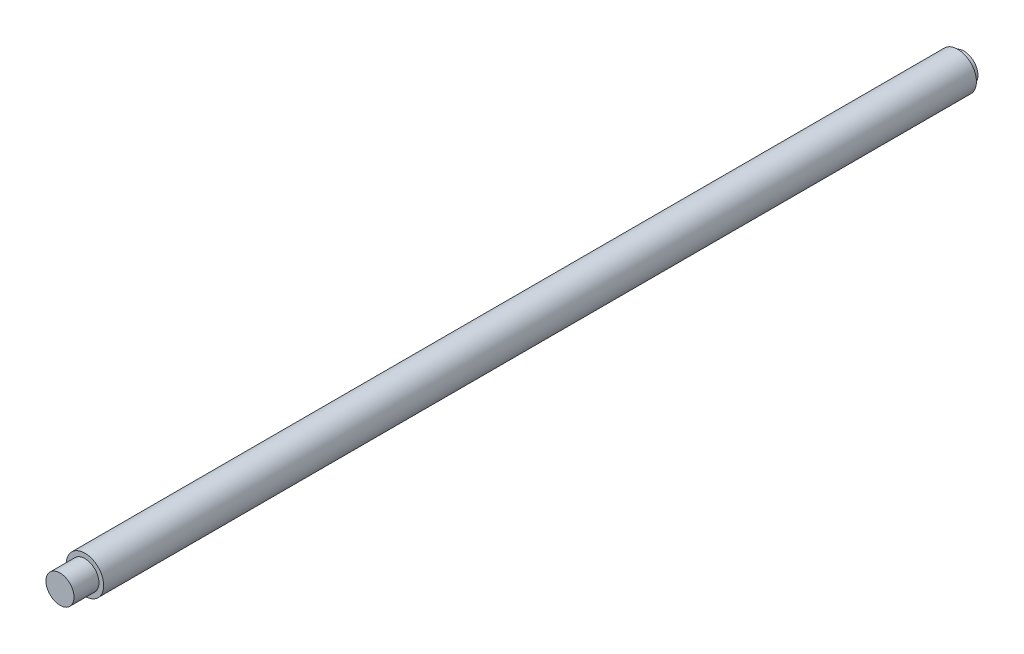
SolidWorks part; units mm, degrees
ref_plane "前视基准面" through (0, 0, 0) normal (0, 0, 1) x (1, 0, 0)
ref_plane "上视基准面" through (0, 0, 0) normal (0, 1, 0) x (1, 0, 0)
ref_plane "右视基准面" through (0, 0, 0) normal (1, 0, 0) x (0, 0, -1)
sketch "草图1" plane through (0, 0, 0) normal (0, 0, 1) x (1, 0, 0)
  circle A0 centre (0, 0) radius 4.5
  dimension "D1" = 9
extrude "凸台-拉伸1" add sketch "草图1" along normal blind 2
sketch "草图2" plane through (0, 0, 2) normal (0, 0, 1) x (1, 0, 0)
  circle A0 centre (0, 0) radius 6
  dimension "D1" = 12
extrude "凸台-拉伸2" add sketch "草图2" along normal blind 280
sketch "草图3" plane through (0, 0, 282) normal (0, 0, 1) x (1, 0, 0)
  circle A0 centre (0, 0) radius 4.5
  dimension "D1" = 9
extrude "凸台-拉伸3" add sketch "草图3" along normal blind 8
